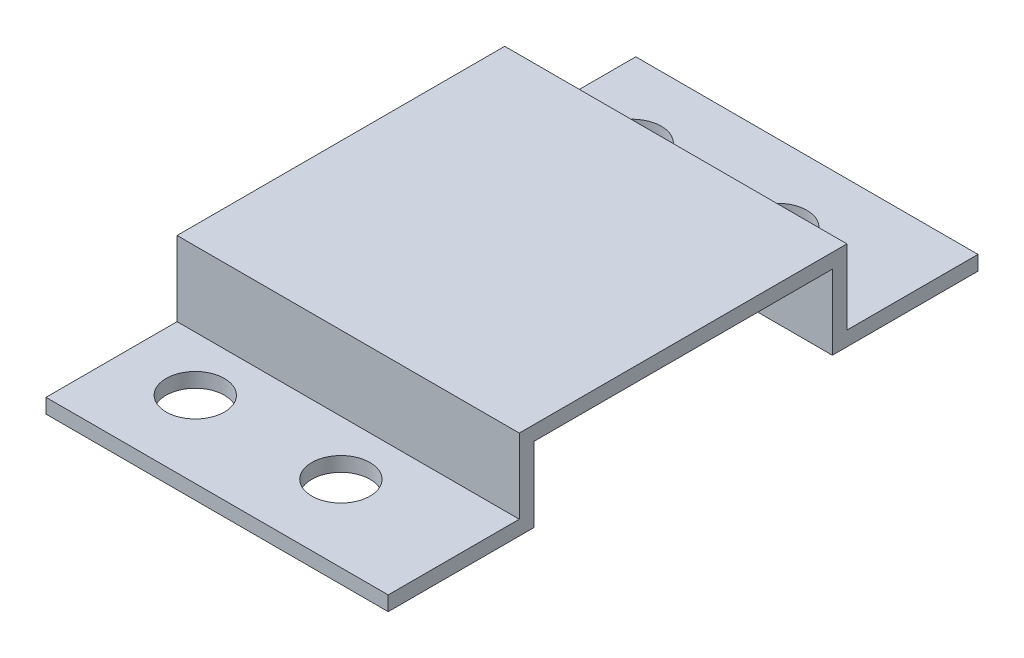
SolidWorks part; units mm, degrees
ref_plane "Спереди" through (0, 0, 0) normal (0, 0, 1) x (1, 0, 0)
ref_plane "Сверху" through (0, 0, 0) normal (0, 1, 0) x (1, 0, 0)
ref_plane "Справа" through (0, 0, 0) normal (1, 0, 0) x (0, 0, -1)
sketch "Эскиз1" plane through (0, 0, 0) normal (1, 0, 0) x (0, 0, -1)
  line L0 (-40.5, 0) -> (-20.5, 0)
  line L1 (-20.5, 0) -> (-20.5, 10.25)
  line L2 (-20.5, 10.25) -> (20.5, 10.25)
  line L3 (0, 34.2184) -> (0, -23.2759) construction
  line L4 (40.5, 0) -> (20.5, 0)
  line L5 (20.5, 0) -> (20.5, 10.25)
  point P4 (0, 0)
  point P10 (0, 10.25)
  point P11 (0, 0)
  point P12 (0, 0)
  point P13 (0, 0)
extrude "Вытянуть-Тонкостенный1" add sketch "Эскиз1" along normal blind 47 thin thin type one direction wall 2
sketch "Эскиз2" plane through (0, 0, 0) normal (0, -1, 0) x (1, 0, 0)
  circle A0 centre (10, 30) radius 4
  circle A1 centre (30, 30) radius 4
  circle A2 centre (30, -30) radius 4
  circle A3 centre (10, -30) radius 4
  dimension "D1" = 2
  dimension "D2" = 2
extrude "Вырез-Вытянуть1" cut sketch "Эскиз2" against normal blind 10
